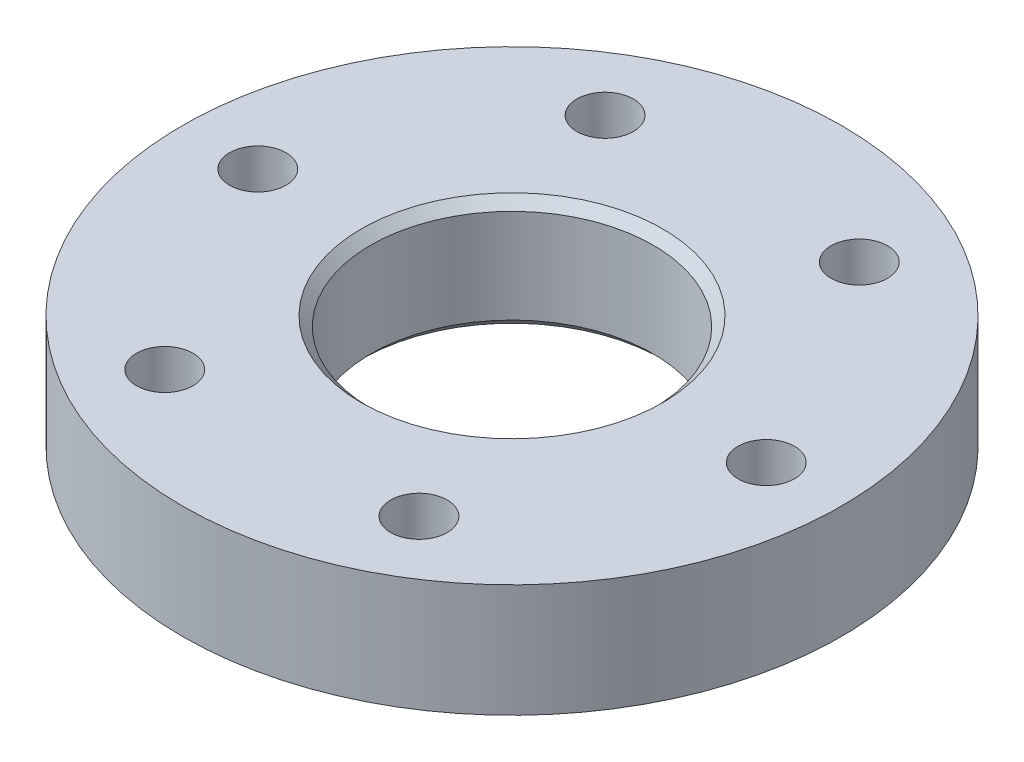
SolidWorks part; units mm, degrees
ref_plane "Front Plane" through (0, 0, 0) normal (0, 0, 1) x (1, 0, 0)
ref_plane "Top Plane" through (0, 0, 0) normal (0, 1, 0) x (1, 0, 0)
ref_plane "Right Plane" through (0, 0, 0) normal (1, 0, 0) x (0, 0, -1)
sketch "Sketch1" plane through (0, 0, 0) normal (0, 1, 0) x (1, 0, 0)
  circle A0 centre (0, 0) radius 13.5 construction
  circle A1 centre (13.5, 0) radius 1.5
  circle A2 centre (6.75, -11.6913) radius 1.5
  circle A3 centre (-6.75, -11.6913) radius 1.5
  circle A4 centre (-13.5, 0) radius 1.5
  circle A5 centre (-6.75, 11.6913) radius 1.5
  circle A6 centre (6.75, 11.6913) radius 1.5
  circle A7 centre (0, 0) radius 17.5
  circle A8 centre (0, 0) radius 7.5
  point P17 (0, 0)
extrude "Boss-Extrude1" add sketch "Sketch1" along normal mid plane 6
sketch "Sketch3" plane through (0, -3, 0) normal (0, -1, 0) x (1, 0, 0)
  circle A0 centre (0, 0) radius 12
  circle A1 centre (0, 0) radius 15
  circle A2 centre (-13.5, 0) radius 1.5 construction
extrude "Boss-Extrude2" add sketch "Sketch3" against normal blind 1.5
chamfer "Chamfer1" distance 0.5 angle 45 2 edges at (0, 3, 7.5) (0, -3, 7.5)
sketch "Sketch4" [suppressed] plane through (0, 4.5, 0) normal (0, 1, 0) x (1, 0, 0)
  circle A0 centre (0, 0) radius 18.5
  circle A1 centre (0, 0) radius 17.5 construction
  circle A2 centre (0, 0) radius 17.5
  dimension "D1" = 1
extrude "Boss-Extrude3" [suppressed] add sketch "Sketch4" against normal blind 2
sketch "Sketch5" [suppressed] plane through (0, -4.5, 0) normal (0, -1, 0) x (-1, 0, 0)
  line L0 (0, 0) -> (-10.8253, -6.25) construction
  line L1 (0, 0) -> (-12.5, 0) construction
  circle A0 centre (0, 0) radius 12.5 construction
  circle A1 centre (-10.8253, -6.25) radius 2.35
  circle A2 centre (-10.8253, 6.25) radius 2.35
  circle A3 centre (0, 12.5) radius 2.35
  circle A4 centre (10.8253, 6.25) radius 2.35
  circle A5 centre (10.8253, -6.25) radius 2.35
  circle A6 centre (0, -12.5) radius 2.35
  point P18 (0, 0)
  dimension "D1" = 4.7
  dimension "D2" = 25
  dimension "D3" = 30
  dimension "D4" = 6
extrude "Cut-Extrude2" [suppressed] cut sketch "Sketch5" against normal blind 4
sketch "Sketch6" [suppressed] plane through (0, -4.5, 0) normal (0, -1, 0) x (1, 0, 0)
  circle A0 centre (0, 0) radius 8
  circle A1 centre (0, 0) radius 14.85
extrude "Boss-Extrude4" [suppressed] add sketch "Sketch6" against normal blind 4
sketch "Sketch7" [suppressed] plane through (0, 4.5, 0) normal (0, 1, 0) x (1, 0, 0)
  circle A0 centre (-6.75, 11.6913) radius 1.5
  circle A1 centre (-13.5, 0) radius 1.5
  circle A2 centre (6.75, 11.6913) radius 1.5
  circle A3 centre (13.5, 0) radius 1.5
  circle A4 centre (6.75, -11.6913) radius 1.5
  circle A5 centre (-6.75, -11.6913) radius 1.5
extrude "Cut-Extrude3" [suppressed] cut sketch "Sketch7" against normal blind 7.5
inserted part "2515N336_Metal Bevel Gear"
move or copy body "Body-Move/Copy10" [suppressed]
equation "\"D5@Sketch1\"=18-3"
